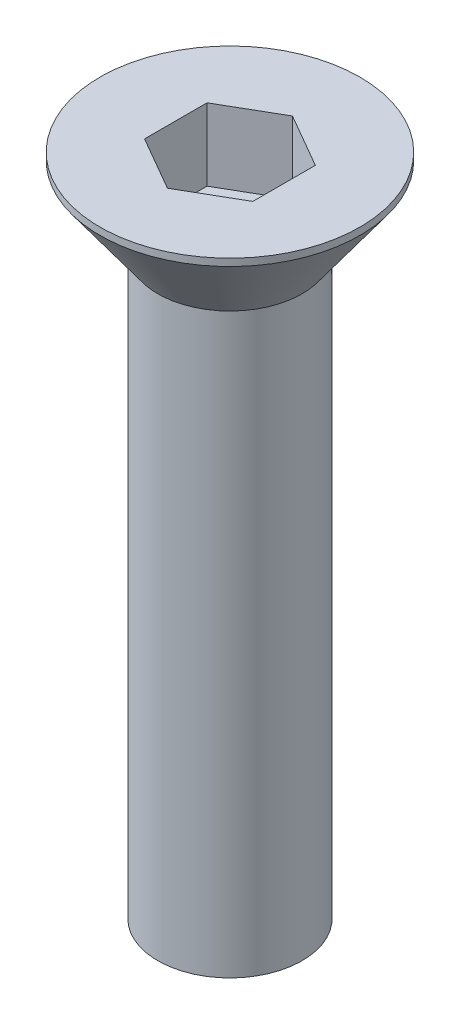
SolidWorks part; units mm, degrees
ref_plane "前视基准面" through (0, 0, 0) normal (0, 0, 1) x (1, 0, 0)
ref_plane "上视基准面" through (0, 0, 0) normal (0, 1, 0) x (1, 0, 0)
ref_plane "右视基准面" through (0, 0, 0) normal (1, 0, 0) x (0, 0, -1)
sketch "草图1" plane through (0, 0, 0) normal (0, 0, 1) x (1, 0, 0)
  line L0 (-4.4256, 0) -> (0, 0) construction
  line L1 (0, 0) -> (0, 2.2273) construction
  line L2 (0, 0) -> (1.8, 0)
  line L3 (1.8, 0) -> (1.8, -0.1)
  line L4 (1.8, -0.1) -> (1, -1.2)
  line L5 (1, -1.2) -> (0, -1.2)
  line L6 (0, -1.2) -> (0, 0)
  dimension "D1" = 1.2
  dimension "D2" = 1.8
  dimension "D3" = 0.1
  dimension "D4" = 1
revolve "旋转1" add sketch "草图1" angle 360 about L1
sketch "草图2" plane through (0, 0, 0) normal (0, 1, 0) x (1, 0, 0)
  line L1 (0, -0.866) -> (0.75, -0.433)
  line L2 (0.75, -0.433) -> (0.75, 0.433)
  line L3 (0.75, 0.433) -> (0, 0.866)
  line L4 (0, 0.866) -> (-0.75, 0.433)
  line L5 (-0.75, 0.433) -> (-0.75, -0.433)
  line L6 (-0.75, -0.433) -> (0, -0.866)
  circle A0 centre (0, 0) radius 0.75 construction
  dimension "D1" = 1.5
extrude "切除-拉伸1" cut sketch "草图2" against normal blind 1
sketch "草图3" plane through (0, -1.2, 0) normal (0, -1, 0) x (1, 0, 0)
  circle A0 centre (0, 0) radius 1
  dimension "D1" = 2
extrude "凸台-拉伸2" add sketch "草图3" along normal blind 8
